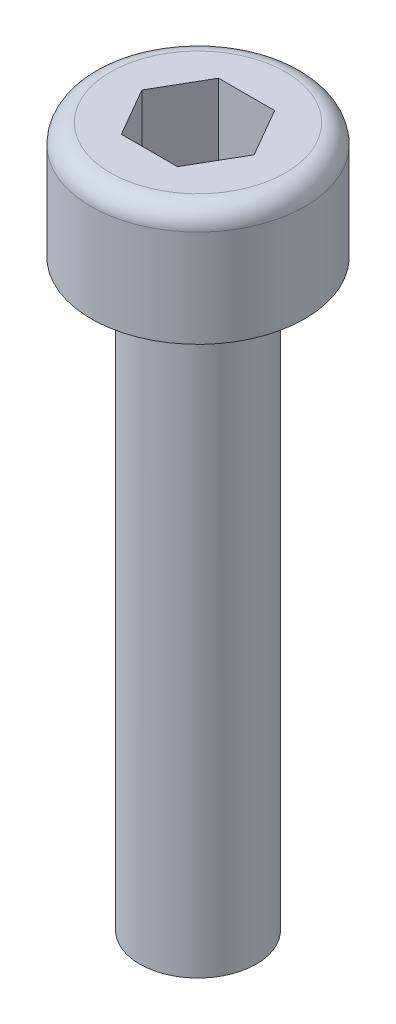
SolidWorks part; units mm, degrees
material "Alloy Steel"
ref_plane "Plane1" through (0, 0, 0) normal (0, 0, 1) x (1, 0, 0)
ref_plane "Plane2" through (0, 0, 0) normal (0, 1, 0) x (1, 0, 0)
ref_plane "Plane3" through (0, 0, 0) normal (1, 0, 0) x (0, 0, -1)
sketch "Sketch1" plane through (0, 0, 0) normal (0, 0, 1) x (1, 0, 0)
  line L0 (0, -15.4019) -> (0, 3)
  line L1 (0, 3) -> (2.25, 3)
  line L2 (2.75, 2.5) -> (2.75, 0)
  line L3 (2.75, 0) -> (1.5, 0)
  line L4 (1.5, 0) -> (1.5, -15)
  line L5 (1.5, -15) -> (0, -15.4019)
  line L6 (0, 3) -> (0, 17) construction
  arc A0 (2.25, 3) -> (2.75, 2.5) centre (2.25, 2.5) cw
  point P10 (2.75, 3)
  dimension "D6" = 0.5
  dimension "D1" = 2.75
  dimension "D2" = 3
  dimension "D3" = 1.5
  dimension "D4" = 15
  dimension "D5" = 75
revolve "Base-Revolve" add sketch "Sketch1" angle 360 about L6
sketch "Sketch2" plane through (0, 3, 0) normal (0, 1, 0) x (-1, 0, 0)
  line L1 (-1.4434, 0) -> (-0.7217, -1.25)
  line L2 (-0.7217, -1.25) -> (0.7217, -1.25)
  line L3 (0.7217, -1.25) -> (1.4434, 0)
  line L4 (1.4434, 0) -> (0.7217, 1.25)
  line L5 (0.7217, 1.25) -> (-0.7217, 1.25)
  line L6 (-0.7217, 1.25) -> (-1.4434, 0)
  circle A0 centre (0, 0) radius 1.25 construction
  dimension "D1" = 2.5
extrude "Cut-Extrude1" cut sketch "Sketch2" against normal blind 2
